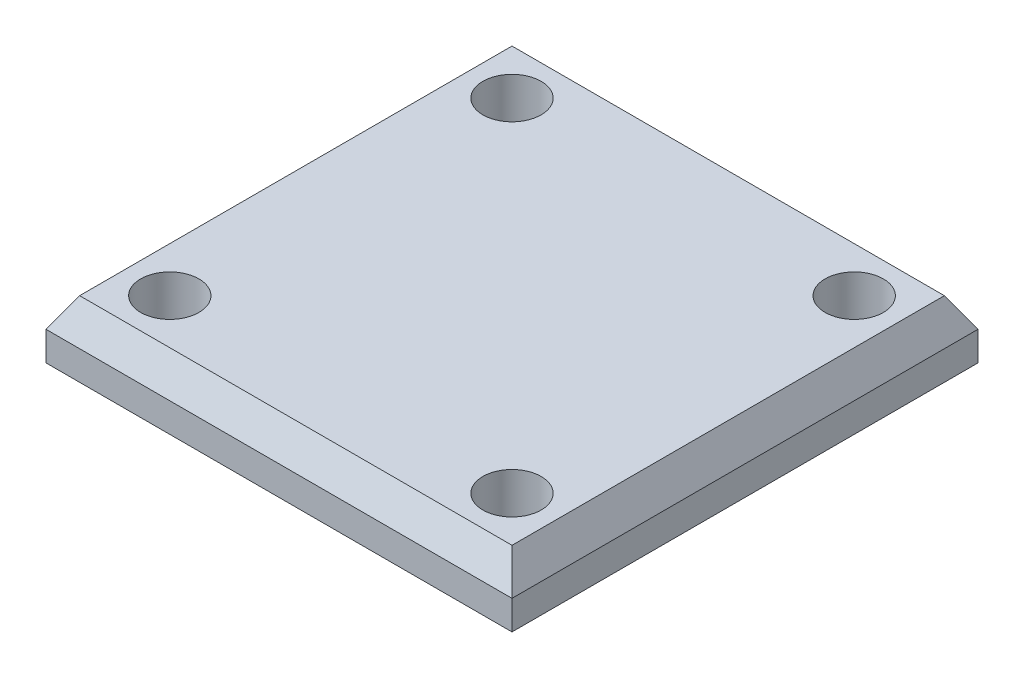
SolidWorks part; units mm, degrees
ref_plane "Front Plane" through (0, 0, 0) normal (0, 0, 1) x (1, 0, 0)
ref_plane "Top Plane" through (0, 0, 0) normal (0, 1, 0) x (1, 0, 0)
ref_plane "Right Plane" through (0, 0, 0) normal (1, 0, 0) x (0, 0, -1)
sketch "Sketch1" plane through (0, 0, 0) normal (0, 1, 0) x (1, 0, 0)
  line L1 (-16, -16) -> (16, -16)
  line L2 (-16, -16) -> (-16, 16)
  line L3 (-16, 16) -> (16, 16)
  line L4 (16, -16) -> (16, 16)
  line L5 (-16, -16) -> (16, 16) construction
  line L6 (-16, 16) -> (16, -16) construction
  point P0 (0, 0)
  dimension "D1" = 32
extrude "Boss-Extrude1" add sketch "Sketch1" along normal blind 4
sketch "Sketch2" plane through (0, 4, 0) normal (0, 1, 0) x (1, 0, 0)
  line L0 (16, 16) -> (-16, 16) construction
  line L1 (-14, -14) -> (14, -14) construction
  line L2 (-14, -14) -> (-14, 14) construction
  line L3 (-14, 14) -> (14, 14) construction
  line L4 (14, -14) -> (14, 14) construction
  line L5 (-14, -14) -> (14, 14) construction
  line L6 (-9.5, 9.5) -> (14, -14) construction
  line L7 (-14, 14) -> (-9.5, 9.5) construction
  line L8 (-9.5, -9.5) -> (9.5, -9.5) construction
  line L9 (-9.5, -9.5) -> (-9.5, 9.5) construction
  line L10 (-9.5, 9.5) -> (9.5, 9.5) construction
  line L11 (9.5, -9.5) -> (9.5, 9.5) construction
  line L12 (-9.5, -9.5) -> (9.5, 9.5) construction
  line L13 (-9.5, 9.5) -> (9.5, -9.5) construction
  line L14 (0, 14) -> (0, -14) construction
  line L15 (-14, 0) -> (14, 0) construction
  circle A0 centre (-11.75, 11.75) radius 2
  circle A1 centre (11.75, 11.75) radius 2
  circle A2 centre (11.75, -11.75) radius 2
  circle A3 centre (-11.75, -11.75) radius 2
  point P0 (0, 0)
  point P8 (0, 0)
  dimension "D3" = 4
  dimension "D1" = 2
  dimension "D2" = 19
extrude "Cut-Extrude1" cut sketch "Sketch2" against normal blind 3
chamfer "Chamfer1" distance 2 angle 30 4 edges at (-16, 4, 0) (0, 4, -16) (16, 4, 0) (0, 4, 16)
